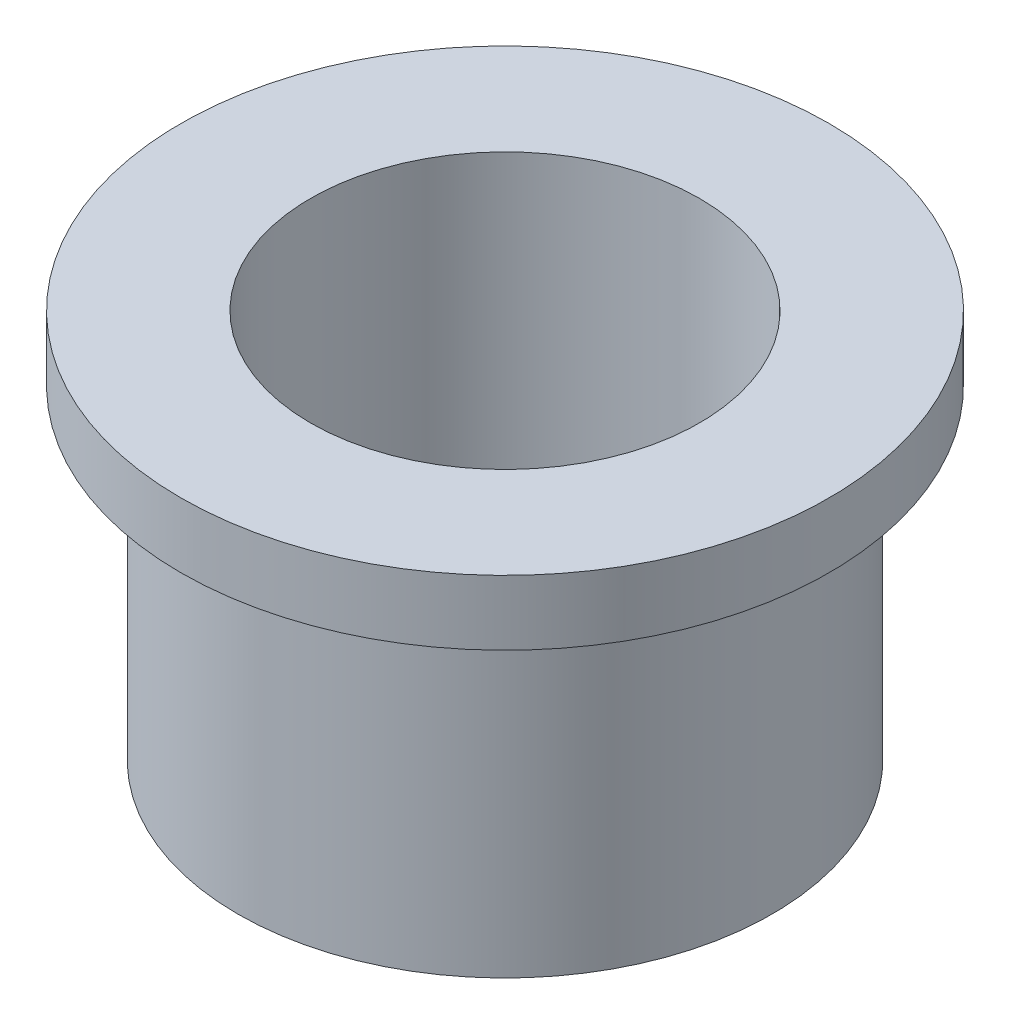
SolidWorks part; units mm, degrees
material "Delrin 2700 NC010, Low Viscosity Acetal Copolymer (SS)"
ref_plane "Front Plane" through (0, 0, 0) normal (0, 0, 1) x (1, 0, 0)
ref_plane "Top Plane" through (0, 0, 0) normal (0, 1, 0) x (1, 0, 0)
ref_plane "Right Plane" through (0, 0, 0) normal (1, 0, 0) x (0, 0, -1)
sketch "Sketch2" plane through (0, 0, 0) normal (1, 0, 0) x (0, 0, -1)
  line L0 (19.05, 0) -> (31.75, 0)
  line L1 (31.75, 0) -> (31.75, -6.35)
  line L2 (31.75, -6.35) -> (26.162, -6.35)
  line L3 (26.162, -6.35) -> (26.162, -38.1)
  line L4 (26.162, -38.1) -> (19.05, -38.1)
  line L5 (19.05, -38.1) -> (19.05, 0)
  line L6 (0, 0) -> (0, -42.4597)
  dimension "D1" = 19.05
  dimension "D2" = 26.162
  dimension "D3" = 31.75
  dimension "D4" = 38.1
  dimension "D5" = 6.35
revolve "Revolve1" add sketch "Sketch2" angle 360 about L6
